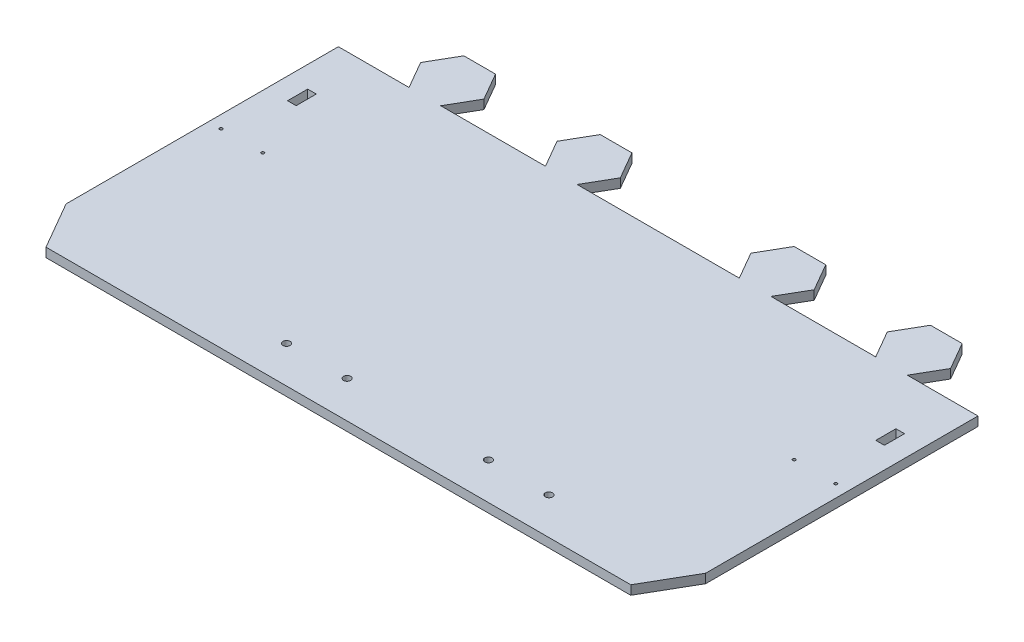
SolidWorks part; units mm, degrees
ref_plane "Front Plane" through (0, 0, 0) normal (0, 0, 1) x (1, 0, 0)
ref_plane "Top Plane" through (0, 0, 0) normal (0, 1, 0) x (1, 0, 0)
ref_plane "Right Plane" through (0, 0, 0) normal (1, 0, 0) x (0, 0, -1)
sketch "Sketch1" plane through (0, 0, 0) normal (0, 1, 0) x (1, 0, 0)
  line L1 (0, 0) -> (444.5, 0)
  line L2 (0, 0) -> (0, 222.25)
  line L3 (0, 222.25) -> (444.5, 222.25)
  line L4 (444.5, 0) -> (444.5, 222.25)
  dimension "D1" = 444.5
  dimension "D2" = 222.25
extrude "Boss-Extrude1" add sketch "Sketch1" along normal blind 6.35
sketch "Sketch3" plane through (0, 6.35, 0) normal (0, 1, 0) x (1, 0, 0)
  line L0 (444.5, 222.25) -> (0, 222.25) construction
  line L1 (82.0941, 241.3) -> (71.0956, 260.35)
  line L2 (71.0956, 260.35) -> (49.0985, 260.35)
  line L3 (49.0985, 260.35) -> (38.1, 241.3)
  line L4 (38.1, 241.3) -> (49.0985, 222.25)
  line L5 (49.0985, 222.25) -> (71.0956, 222.25)
  line L6 (71.0956, 222.25) -> (82.0941, 241.3)
  line L7 (107.4941, 222.25) -> (107.4941, 318.1757) construction
  line L8 (0, 222.25) -> (0, 0) construction
  line L9 (143.8926, 222.25) -> (132.8941, 241.3)
  line L10 (165.8897, 222.25) -> (143.8926, 222.25)
  line L11 (176.8882, 241.3) -> (165.8897, 222.25)
  line L12 (165.8897, 260.35) -> (176.8882, 241.3)
  line L13 (143.8926, 260.35) -> (165.8897, 260.35)
  line L14 (132.8941, 241.3) -> (143.8926, 260.35)
  line L15 (222.25, 0) -> (222.25, 222.25) construction
  line L16 (0, 0) -> (444.5, 0) construction
  line L17 (311.6059, 241.3) -> (300.6074, 260.35)
  line L18 (300.6074, 260.35) -> (278.6103, 260.35)
  line L19 (278.6103, 260.35) -> (267.6118, 241.3)
  line L20 (267.6118, 241.3) -> (278.6103, 222.25)
  line L21 (278.6103, 222.25) -> (300.6074, 222.25)
  line L22 (300.6074, 222.25) -> (311.6059, 241.3)
  line L23 (373.4044, 222.25) -> (362.4059, 241.3)
  line L24 (395.4015, 222.25) -> (373.4044, 222.25)
  line L25 (406.4, 241.3) -> (395.4015, 222.25)
  line L26 (395.4015, 260.35) -> (406.4, 241.3)
  line L27 (373.4044, 260.35) -> (395.4015, 260.35)
  line L28 (362.4059, 241.3) -> (373.4044, 260.35)
  circle A0 centre (60.097, 241.3) radius 19.05 construction
  circle A1 centre (154.8911, 241.3) radius 19.05 construction
  circle A2 centre (289.6089, 241.3) radius 19.05 construction
  circle A3 centre (384.403, 241.3) radius 19.05 construction
  dimension "D1" = 19.05
  dimension "D2" = 38.1
  dimension "D3" = 25.4
extrude "Boss-Extrude2" add sketch "Sketch3" against normal up to surface (6.35 mm away) up to face at (222.25, 0, -111.125)
sketch "Sketch4" plane through (0, 6.35, 0) normal (0, 1, 0) x (1, 0, 0)
  line L18 (0, 0) -> (0, 32.9956)
  line L19 (0, 32.9956) -> (19.05, 0)
  line L20 (19.05, 0) -> (0, 0)
  line L21 (444.5, 0) -> (444.5, 32.9956)
  line L22 (444.5, 32.9956) -> (425.45, 0)
  line L23 (0, 0) -> (444.5, 0) construction
  line L24 (425.45, 0) -> (444.5, 0)
  dimension "D1" = 38.1
  dimension "D2" = 19.05
extrude "Cut-Extrude1" cut sketch "Sketch4" against normal through all
sketch "Sketch5" plane through (0, 6.35, 0) normal (0, 1, 0) x (1, 0, 0)
  line L0 (444.5, 25.65) -> (0, 25.65) construction
  line L1 (444.5, 32.9956) -> (444.5, 222.25) construction
  line L2 (0, 222.25) -> (0, 32.9956) construction
  line L3 (19.05, 0) -> (425.45, 0) construction
  circle A0 centre (342.9, 25.65) radius 2.5
  circle A1 centre (300.84, 25.65) radius 2.5
  circle A2 centre (202.66, 25.65) radius 2.5
  circle A3 centre (160.6, 25.65) radius 2.5
  dimension "D2" = 5
  dimension "D1" = 25.65
  dimension "D3" = 101.6
  dimension "D4" = 42.06
  dimension "D5" = 42.06
  dimension "D6" = 98.18
extrude "Cut-Extrude2" cut sketch "Sketch5" against normal through all
sketch "Sketch6" plane through (0, 6.35, 0) normal (0, 1, 0) x (1, 0, 0)
  line L0 (444.5, 32.9956) -> (444.5, 222.25) construction
  line L1 (19.05, 0) -> (425.45, 0) construction
  line L2 (222.25, 0) -> (222.25, 222.25) construction
  line L4 (406.912, 132.0659) -> (435.852, 132.0659) construction
  line L5 (143.8926, 222.25) -> (71.0956, 222.25) construction
  line L6 (222.25, 222.25) -> (444.5, 222.25) construction
  line L7 (222.25, 222.25) -> (0, 222.25) construction
  circle A0 centre (406.912, 132.0659) radius 1.016
  circle A1 centre (37.588, 132.0659) radius 1.016
  circle A2 centre (435.852, 132.0659) radius 1.016
  circle A3 centre (8.648, 132.0659) radius 1.016
  dimension "D1" = 2.032
  dimension "D2" = 37.588
  dimension "D3" = 132.0659
  dimension "D4" = 28.94
extrude "Cut-Extrude3" cut sketch "Sketch6" against normal through all
sketch "Sketch7" plane through (0, 6.35, 0) normal (0, 1, 0) x (1, 0, 0)
  line L0 (444.5, 32.9956) -> (444.5, 222.25) construction
  line L1 (429.641, 186.061) -> (423.672, 186.061)
  line L2 (429.641, 186.061) -> (429.641, 172.061)
  line L3 (429.641, 172.061) -> (423.672, 172.061)
  line L4 (423.672, 186.061) -> (423.672, 172.061)
  line L5 (429.641, 186.061) -> (423.672, 172.061) construction
  line L6 (429.641, 172.061) -> (423.672, 186.061) construction
  line L7 (19.05, 0) -> (425.45, 0) construction
  line L8 (222.25, 0) -> (222.25, 222.25) construction
  line L10 (14.859, 172.061) -> (20.828, 186.061) construction
  line L11 (14.859, 186.061) -> (20.828, 172.061) construction
  line L12 (20.828, 186.061) -> (20.828, 172.061)
  line L13 (14.859, 172.061) -> (20.828, 172.061)
  line L14 (14.859, 186.061) -> (14.859, 172.061)
  line L15 (14.859, 186.061) -> (20.828, 186.061)
  line L16 (0, 222.25) -> (444.5, 222.25) construction
  point P4 (426.6565, 179.061)
  point P17 (17.8435, 179.061)
  dimension "D1" = 14
  dimension "D2" = 5.969
  dimension "D3" = 14.859
  dimension "D4" = 172.061
extrude "Cut-Extrude4" cut sketch "Sketch7" against normal through all
